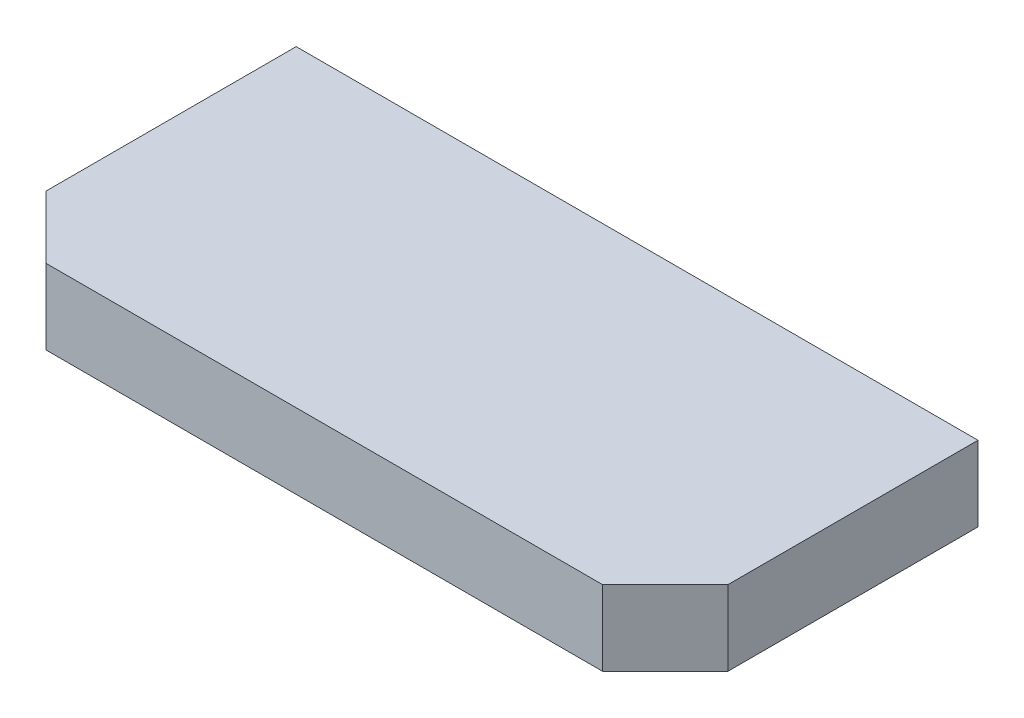
SolidWorks part; units mm, degrees
material "Plain Carbon Steel"
ref_plane "Front Plane" through (0, 0, 0) normal (0, 0, 1) x (1, 0, 0)
ref_plane "Top Plane" through (0, 0, 0) normal (0, 1, 0) x (1, 0, 0)
ref_plane "Right Plane" through (0, 0, 0) normal (1, 0, 0) x (0, 0, -1)
sketch "Sketch1" plane through (0, 0, 0) normal (0, 1, 0) x (1, 0, 0)
  line L0 (-27.25, -7.5) -> (-22.25, -12.5)
  line L1 (-22.25, -12.5) -> (22.25, -12.5)
  line L2 (-27.25, -7.5) -> (-27.25, 12.5)
  line L3 (-27.25, 12.5) -> (27.25, 12.5)
  line L4 (27.25, -7.5) -> (27.25, 12.5)
  line L5 (-27.25, -12.5) -> (27.25, 12.5) construction
  line L6 (-27.25, 12.5) -> (27.25, -12.5) construction
  line L7 (22.25, -12.5) -> (27.25, -7.5)
  point P0 (0, 0)
  dimension "D1" = 54.5
  dimension "D2" = 25
extrude "Boss-Extrude1" add sketch "Sketch1" along normal blind 6
